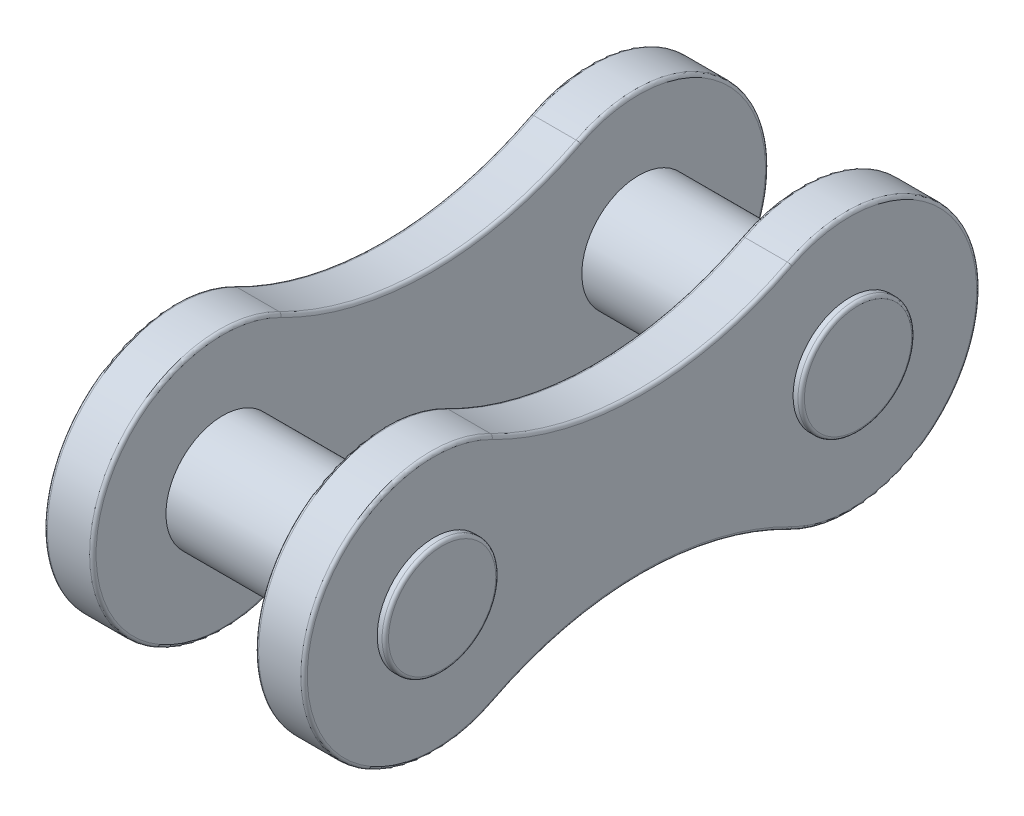
SolidWorks part; units mm, degrees
material "1060 Alloy"
ref_plane "Front Plane" through (0, 0, 0) normal (0, 0, 1) x (1, 0, 0)
ref_plane "Top Plane" through (0, 0, 0) normal (0, 1, 0) x (1, 0, 0)
ref_plane "Right Plane" through (0, 0, 0) normal (1, 0, 0) x (0, 0, -1)
sketch "Sketch5" plane through (0, 0, 0) normal (1, 0, 0) x (0, 0, -1)
  line L0 (0, -1454.1638) -> (0, 3744.1855) construction
  line L1 (6.3985, 0) -> (-6.3985, 0) construction
  arc A0 (-4.5704, 3.5578) -> (-4.5704, -3.5578) centre (-6.3985, 0) ccw
  circle A1 centre (-6.3985, 0) radius 1.75
  circle A2 centre (6.3985, 0) radius 1.75
  arc A3 (4.5704, 3.5578) -> (4.5704, -3.5578) centre (6.3985, 0) cw
  arc A4 (-4.5704, 3.5578) -> (4.5704, 3.5578) centre (0, 12.4523) ccw
  arc A5 (-4.5704, -3.5578) -> (4.5704, -3.5578) centre (0, -12.4523) cw
  dimension "D1" = 8
  dimension "D2" = 3.5
  dimension "D4" = 10
  dimension "D3" = 12.797
extrude "Boss-Extrude2" add sketch "Sketch5" along normal blind 1.5 from offset 2.5
sketch "Sketch6" plane through (0, 0, 0) normal (1, 0, 0) x (0, 0, -1)
  circle A0 centre (6.3985, 0) radius 1.75 construction
  circle A1 centre (-6.3985, 0) radius 1.75 construction
  circle A2 centre (6.3985, 0) radius 1.75
  circle A3 centre (-6.3985, 0) radius 1.75
  arc A4 (-4.5704, 3.5578) -> (4.5704, 3.5578) centre (0, 12.4523) ccw
  arc A5 (-4.5704, 3.5578) -> (-4.5704, -3.5578) centre (-6.3985, 0) ccw
  arc A6 (4.5704, -3.5578) -> (-4.5704, -3.5578) centre (0, -12.4523) ccw
  arc A7 (4.5704, -3.5578) -> (4.5704, 3.5578) centre (6.3985, 0) ccw
  arc A8 (-4.5704, 3.5578) -> (4.5704, 3.5578) centre (0, 12.4523) ccw
  arc A9 (-4.5704, 3.5578) -> (-4.5704, -3.5578) centre (-6.3985, 0) ccw
  arc A10 (4.5704, -3.5578) -> (-4.5704, -3.5578) centre (0, -12.4523) ccw
  arc A11 (4.5704, -3.5578) -> (4.5704, 3.5578) centre (6.3985, 0) ccw
  dimension "D1" = 0
extrude "Boss-Extrude3" add sketch "Sketch6" against normal blind 1.5 from offset 2.5 separate body offset against normal yes
sketch "Sketch7" plane through (0, 0, 0) normal (1, 0, 0) x (0, 0, -1)
  circle A0 centre (6.3985, 0) radius 1.75 construction
  circle A1 centre (-6.3985, 0) radius 1.75 construction
  circle A2 centre (6.3985, 0) radius 1.75
  circle A3 centre (-6.3985, 0) radius 1.75
extrude "Boss-Extrude4" add sketch "Sketch7" along normal mid plane 8.5
fillet "Fillet1" radius 0.1 20 edges at (4, 0, -10.3985) (4, -2.4523, 0) (4, 0, 10.3985) (2.5, 0, -10.3985) (2.5, -2.4523, 0) (2.5, 0, 10.3985) (-4, 0, -10.3985) (-4, -2.4523, 0) (-4, 0, 10.3985) (-2.5, 0, -10.3985) (-2.5, -2.4523, 0) (-2.5, 0, 10.3985) (4, 2.4523, 0) (2.5, 2.4523, 0) (-4, 2.4523, 0) (-2.5, 2.4523, 0) (-4.25, 0, -8.1485) (-4.25, 0, 4.6485) (4.25, 0, -8.1485) (4.25, 0, 4.6485)
